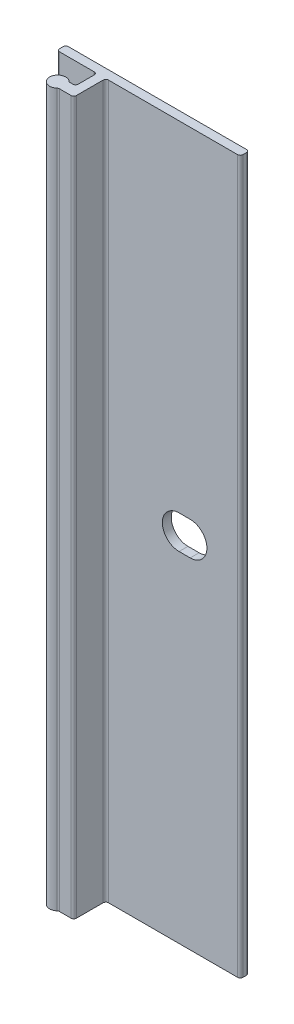
SolidWorks part; units mm, degrees
material "6463-T6"
ref_plane "Front Plane" through (0, 0, 0) normal (0, 0, 1) x (1, 0, 0)
ref_plane "Top Plane" through (0, 0, 0) normal (0, 1, 0) x (1, 0, 0)
ref_plane "Right Plane" through (0, 0, 0) normal (1, 0, 0) x (0, 0, -1)
sketch "Sketch2" plane through (0, 0, 0) normal (0, 1, 0) x (1, 0, 0)
  line L0 (0, -55) -> (0, 55) construction
  line L16 (-5.334, 0) -> (20.066, 0)
  line L18 (20.447, -0.381) -> (20.447, -0.889)
  line L19 (20.066, -1.27) -> (1.651, -1.27)
  line L20 (1.27, -1.651) -> (1.27, -5.461)
  line L52 (0, -1.651) -> (0, -3.937)
  line L53 (-55, 0) -> (55, 0) construction
  line L54 (-0.77, -4.318) -> (-0.381, -4.318)
  line L55 (-0.77, -5.842) -> (0.889, -5.842)
  line L57 (-0.381, -1.27) -> (-5.334, -1.27)
  line L58 (-5.715, -0.889) -> (-5.715, -0.381)
  arc A11 (20.066, 0) -> (20.447, -0.381) centre (20.066, -0.381) cw
  arc A12 (20.447, -0.889) -> (20.066, -1.27) centre (20.066, -0.889) cw
  arc A19 (1.651, -1.27) -> (1.27, -1.651) centre (1.651, -1.651) ccw
  arc A20 (-1.022, -4.2227) -> (-1.022, -5.9373) centre (-1.778, -5.08) ccw
  arc A23 (0, -3.937) -> (-0.381, -4.318) centre (-0.381, -3.937) cw
  arc A26 (-0.77, -5.842) -> (-1.022, -5.9373) centre (-0.77, -6.223) ccw
  arc A27 (-0.77, -4.318) -> (-1.022, -4.2227) centre (-0.77, -3.937) cw
  arc A28 (-5.715, -0.381) -> (-5.334, 0) centre (-5.334, -0.381) cw
  arc A29 (-5.334, -1.27) -> (-5.715, -0.889) centre (-5.334, -0.889) cw
  arc A30 (-0.381, -1.27) -> (0, -1.651) centre (-0.381, -1.651) cw
  arc A31 (0.889, -5.842) -> (1.27, -5.461) centre (0.889, -5.461) ccw
  dimension "D1" = 26.162
  dimension "D7" = 5.08
  dimension "D6" = 5.842
  dimension "D10" = 1.524
  dimension "D9" = 1.778
  dimension "D3" = 0.381
  dimension "D8" = 1.143
  dimension "D2" = 1.27
  dimension "D4" = 5.715
  dimension "D5" = 1.27
extrude "Boss-Extrude1" add sketch "Sketch2" along normal mid plane 101.6
sketch "Sketch3" plane through (0, 0, 1.27) normal (0, 0, 1) x (1, 0, 0)
  line L0 (11.7157, 0) -> (13.3033, 0) construction
  line L1 (11.7157, 2.3813) -> (13.3032, 2.3813)
  line L2 (11.7157, -2.3813) -> (13.3032, -2.3812)
  line L3 (20.447, 50.8) -> (20.447, -50.8) construction
  arc A0 (11.7157, 2.3813) -> (11.7157, -2.3813) centre (11.7157, 0) ccw
  arc A1 (13.3032, -2.3812) -> (13.3032, 2.3813) centre (13.3033, 0) ccw
  point P3 (12.5095, 0)
  dimension "D1" = 4.7625
  dimension "D2" = 6.35
  dimension "D3" = 7.9375
extrude "Cut-Extrude1" cut sketch "Sketch3" against normal through all
